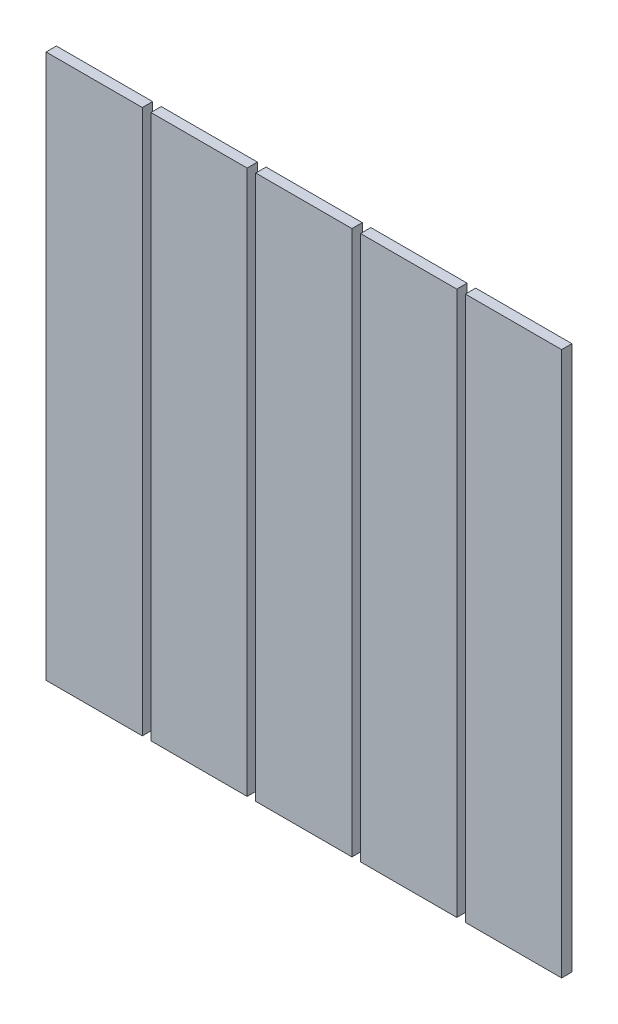
SolidWorks part; units mm, degrees
material "Pino"
ref_plane "Alzado" through (0, 0, 0) normal (0, 0, 1) x (1, 0, 0)
ref_plane "Planta" through (0, 0, 0) normal (0, 1, 0) x (1, 0, 0)
ref_plane "Vista lateral" through (0, 0, 0) normal (1, 0, 0) x (0, 0, -1)
sketch "Croquis1" plane through (0, 0, 0) normal (0, 0, 1) x (1, 0, 0)
  line L1 (0, 0) -> (-900, 0)
  line L2 (0, 0) -> (0, 950)
  line L3 (0, 950) -> (-900, 950)
  line L4 (-900, 0) -> (-900, 950)
  dimension "D1" = 900
  dimension "D2" = 950
extrude "Saliente-Extruir1" add sketch "Croquis1" along normal blind 18
sketch "Croquis2" plane through (0, 0, 18) normal (0, 0, 1) x (1, 0, 0)
  line L0 (-732, 950) -> (-732, 0)
  line L1 (0, 950) -> (-900, 950) construction
  line L2 (-900, 0) -> (0, 0) construction
  line L3 (-168, 950) -> (-168, 0)
  line L4 (-351, 950) -> (-351, 0)
  line L5 (-549, 950) -> (-549, 0)
  line L6 (-900, 950) -> (-900, 0) construction
  line L7 (-732, 950) -> (-717, 950)
  line L8 (-717, 950) -> (-717, 0)
  line L9 (-534, 0) -> (-534, 950)
  line L10 (-366, 950) -> (-366, 0)
  line L11 (-183, 950) -> (-183, 0)
  line L12 (-732, 0) -> (-717, 0)
  line L13 (-549, 950) -> (-534, 950)
  line L14 (-549, 0) -> (-534, 0)
  line L15 (-366, 0) -> (-351, 0)
  line L16 (-183, 0) -> (-168, 0)
  line L17 (-366, 950) -> (-351, 950)
  line L18 (-183, 950) -> (-168, 950)
  dimension "D1" = 168
  dimension "D2" = 15
  dimension "D3" = 168
  dimension "D4" = 15
  dimension "D5" = 168
  dimension "D6" = 15
  dimension "D7" = 15
  dimension "D8" = 168
extrude "Cortar-Extruir1" cut sketch "Croquis2" against normal blind 18
